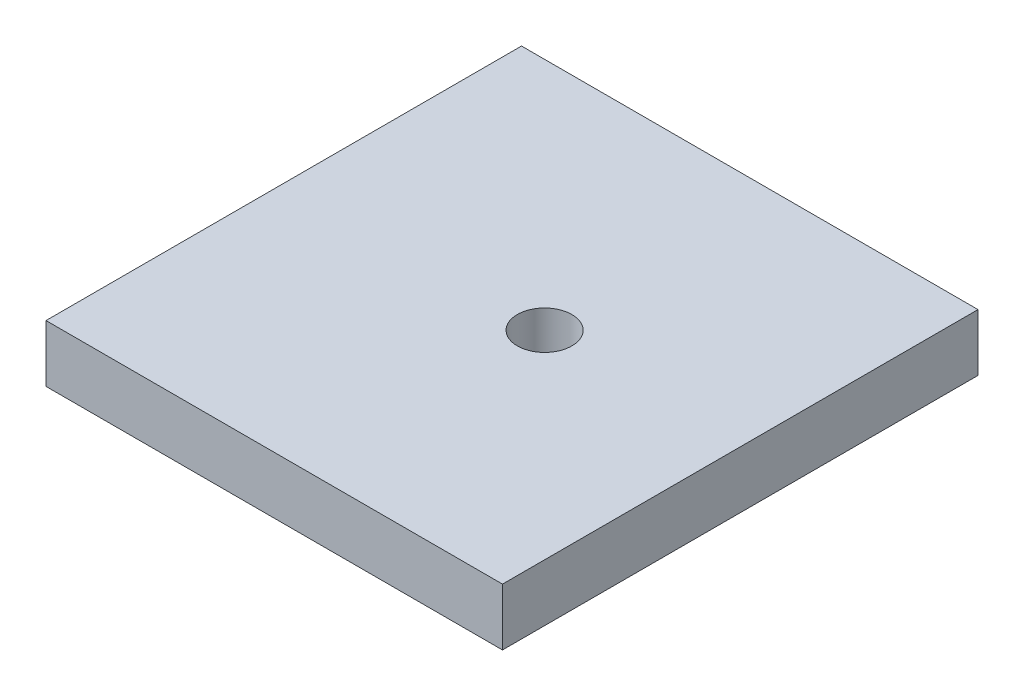
SolidWorks part; units mm, degrees
ref_plane "Front Plane" through (0, 0, 0) normal (0, 0, 1) x (1, 0, 0)
ref_plane "Top Plane" through (0, 0, 0) normal (0, 1, 0) x (1, 0, 0)
ref_plane "Right Plane" through (0, 0, 0) normal (1, 0, 0) x (0, 0, -1)
sketch "Sketch1" plane through (0, 0, 0) normal (0, 1, 0) x (1, 0, 0)
  line L1 (-24.6645, 9.615) -> (11.3355, 9.615)
  line L2 (-24.6645, 9.615) -> (-24.6645, -27.885)
  line L3 (-24.6645, -27.885) -> (11.3355, -27.885)
  line L4 (11.3355, 9.615) -> (11.3355, -27.885)
  dimension "D1" = 36
  dimension "D2" = 37.5
extrude "Boss-Extrude1" add sketch "Sketch1" along normal blind 4.5
sketch "Sketch2" plane through (0, 4.5, 0) normal (0, 1, 0) x (1, 0, 0)
  line L0 (-24.6645, -27.885) -> (11.3355, -27.885) construction
  line L1 (-24.6645, 9.615) -> (-24.6645, -27.885) construction
  circle A0 centre (-4.3445, -8.885) radius 2.15
  point P2 (-6.6645, -27.885)
  dimension "D1" = 19
  dimension "D2" = 4.3
  dimension "D3" = 20.32
extrude "Cut-Extrude1" cut sketch "Sketch2" against normal through all
